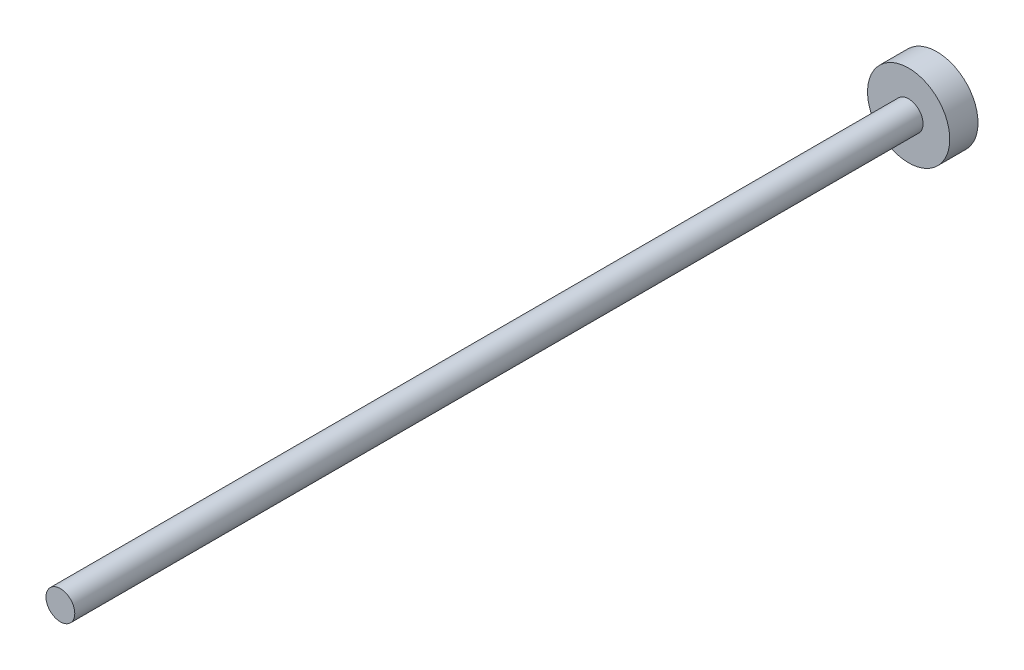
SolidWorks part; units mm, degrees
ref_plane "Front Plane" through (0, 0, 0) normal (0, 0, 1) x (1, 0, 0)
ref_plane "Top Plane" through (0, 0, 0) normal (0, 1, 0) x (1, 0, 0)
ref_plane "Right Plane" through (0, 0, 0) normal (1, 0, 0) x (0, 0, -1)
sketch "Sketch1" plane through (0, 0, 0) normal (0, 0, 1) x (1, 0, 0)
  circle A0 centre (0, 0) radius 4.65
extrude "Boss-Extrude1" add sketch "Sketch1" along normal blind 3.2
sketch "Sketch2" plane through (0, 0, 3.2) normal (0, 0, 1) x (1, 0, 0)
  circle A0 centre (0, 0) radius 1.63
extrude "Boss-Extrude2" add sketch "Sketch2" along normal blind 96
